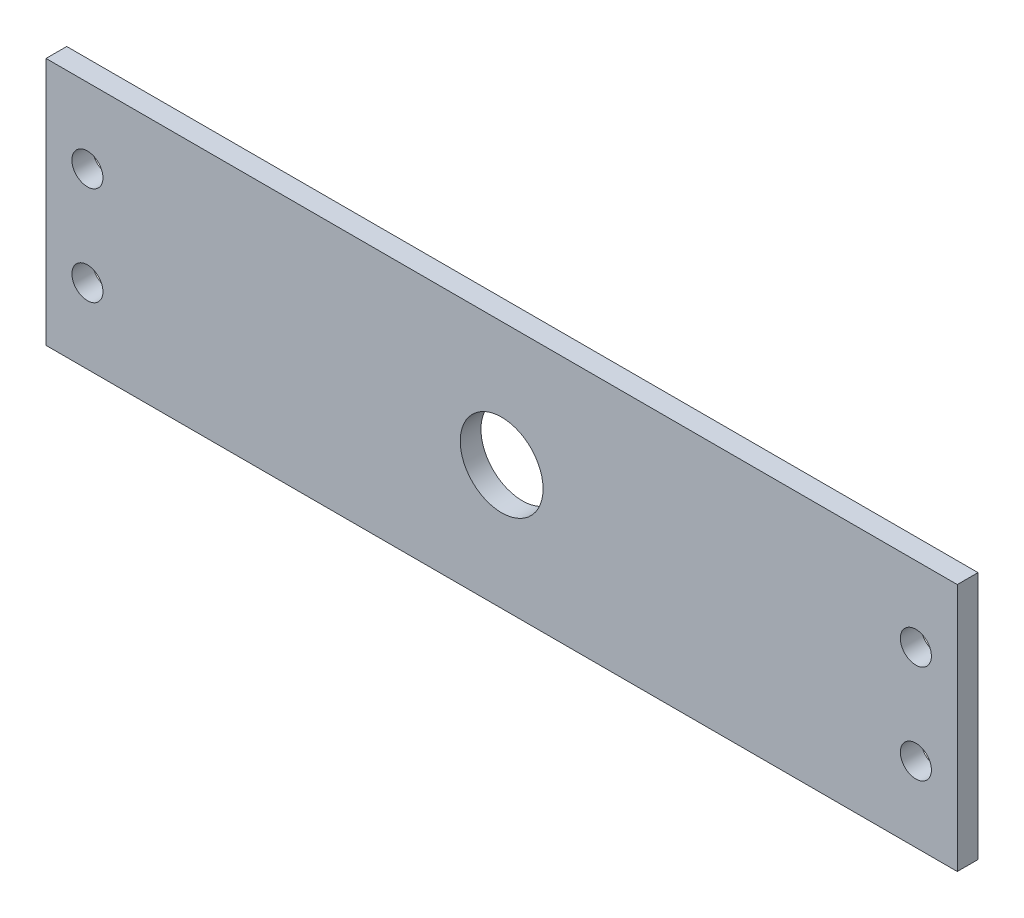
SolidWorks part; units mm, degrees
ref_plane "Front Plane" through (0, 0, 0) normal (0, 0, 1) x (1, 0, 0)
ref_plane "Top Plane" through (0, 0, 0) normal (0, 1, 0) x (1, 0, 0)
ref_plane "Right Plane" through (0, 0, 0) normal (1, 0, 0) x (0, 0, -1)
sketch "Sketch1" plane through (0, 0, 0) normal (0, 0, 1) x (1, 0, 0)
  line L1 (0, 0) -> (558.8, 0)
  line L2 (0, 0) -> (0, 152.4)
  line L3 (0, 152.4) -> (558.8, 152.4)
  line L4 (558.8, 0) -> (558.8, 152.4)
  dimension "D1" = 152.4
  dimension "D2" = 558.8
extrude "Boss-Extrude1" add sketch "Sketch1" along normal blind 12.7
sketch "Sketch2" plane through (0, 0, 12.7) normal (0, 0, 1) x (1, 0, 0)
  line L0 (533.4, 0) -> (533.4, 225.0982) construction
  line L1 (0, 0) -> (558.8, 0) construction
  line L2 (558.8, 45.974) -> (533.4, 45.974) construction
  line L3 (558.8, 0) -> (558.8, 152.4) construction
  line L4 (558.8, 106.426) -> (533.4, 106.426) construction
  line L5 (279.4, 152.4) -> (279.4, 0) construction
  line L6 (558.8, 152.4) -> (0, 152.4) construction
  line L7 (0, 76.2) -> (558.8, 76.2) construction
  line L8 (0, 152.4) -> (0, 0) construction
  circle A0 centre (533.4, 45.974) radius 9.525
  circle A1 centre (533.4, 106.426) radius 9.525
  circle A2 centre (25.4, 45.974) radius 9.525
  circle A3 centre (25.4, 106.426) radius 9.525
  circle A4 centre (279.4, 76.2) radius 25.4
  dimension "D4" = 19.05
  dimension "D2" = 50.8
  dimension "D1" = 45.974
  dimension "D3" = 25.4
extrude "Cut-Extrude1" cut sketch "Sketch2" against normal through all
